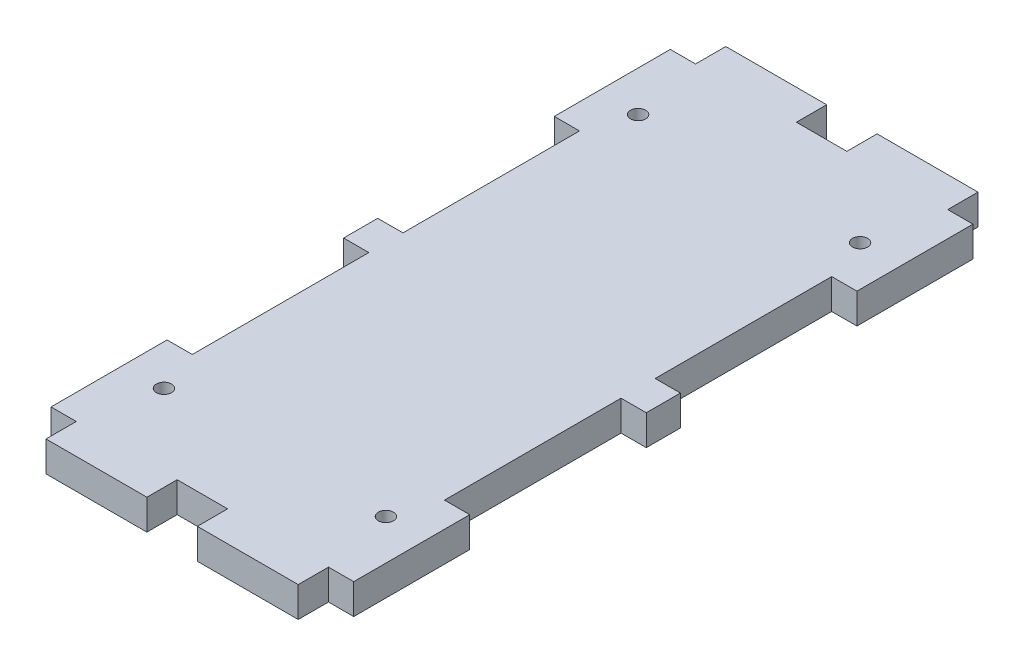
SolidWorks part; units mm, degrees
ref_plane "Plan de face" through (0, 0, 0) normal (0, 0, 1) x (1, 0, 0)
ref_plane "Plan de dessus" through (0, 0, 0) normal (0, 1, 0) x (1, 0, 0)
ref_plane "Plan de droite" through (0, 0, 0) normal (1, 0, 0) x (0, 0, -1)
sketch "Esquisse1" plane through (0, 0, 0) normal (0, 1, 0) x (1, 0, 0)
  line L0 (0, 89.2093) -> (0, -94.1785) construction
  line L1 (-30, 61.38) -> (30, 61.38)
  line L2 (-30, 61.38) -> (-30, -61.38)
  line L3 (-30, -61.38) -> (30, -61.38)
  line L4 (30, 61.38) -> (30, -61.38)
  dimension "D1" = 60
  dimension "D2" = 122.76
  dimension "D3" = 61.38
  dimension "D4" = 30
extrude "Boss.-Extru.1" add sketch "Esquisse1" along normal blind 6
sketch "Esquisse2" plane through (0, 6, 0) normal (0, 1, 0) x (1, 0, 0)
  line L0 (30, 61.38) -> (-30, 61.38) construction
  line L1 (-25, 61.38) -> (-5, 61.38)
  line L2 (-25, 61.38) -> (-25, 67.38)
  line L3 (-25, 67.38) -> (-5, 67.38)
  line L4 (-5, 61.38) -> (-5, 67.38)
  line L6 (5, 61.38) -> (25, 61.38)
  line L7 (5, 61.38) -> (5, 67.38)
  line L8 (5, 67.38) -> (25, 67.38)
  line L9 (25, 61.38) -> (25, 67.38)
  line L10 (-30, 61.38) -> (-30, -61.38) construction
  line L11 (30, -61.38) -> (30, 61.38) construction
  line L12 (-114.0924, 0) -> (165.6917, 0) construction
  line L13 (25, -61.38) -> (25, -67.38)
  line L14 (5, -67.38) -> (25, -67.38)
  line L15 (5, -61.38) -> (5, -67.38)
  line L16 (5, -61.38) -> (25, -61.38)
  line L17 (-5, -61.38) -> (-5, -67.38)
  line L18 (-25, -67.38) -> (-5, -67.38)
  line L19 (-25, -61.38) -> (-25, -67.38)
  line L20 (-25, -61.38) -> (-5, -61.38)
  dimension "D1" = 6
  dimension "D2" = 20
  dimension "D3" = 6
  dimension "D4" = 20
  dimension "D5" = 5
  dimension "D6" = 5
extrude "Boss.-Extru.2" add sketch "Esquisse2" against normal blind 6
sketch "Esquisse3" plane through (0, 6, 0) normal (0, 1, 0) x (1, 0, 0)
  line L0 (73.2715, 0) -> (-73.7315, 0) construction
  line L1 (-60.2107, 47) -> (82.7649, 47) construction
  line L2 (-25, 61.38) -> (-30, 61.38) construction
  line L3 (30, -61.38) -> (30, 61.38) construction
  line L4 (-30, 61.38) -> (-30, -61.38) construction
  circle A0 centre (22, 47) radius 1.5
  circle A1 centre (-22, 47) radius 1.5
  circle A2 centre (-22, -47) radius 1.5
  circle A3 centre (22, -47) radius 1.5
  point P5 (-27.5, 61.38)
  dimension "D3" = 3
  dimension "D4" = 3
  dimension "D5" = 44
  dimension "D6" = 94
  dimension "D1" = 14.38
  dimension "D2" = 8
  dimension "D7" = 8
extrude "Enlèv. mat.-Extru.1" cut sketch "Esquisse3" against normal blind 6
sketch "Esquisse4" plane through (0, 6, 0) normal (0, 1, 0) x (1, 0, 0)
  line L0 (-30, 61.38) -> (-30, -61.38) construction
  line L1 (-30, -3.38) -> (-25, -3.38)
  line L2 (-30, -3.38) -> (-30, -38.38)
  line L3 (-30, -38.38) -> (-25, -38.38)
  line L4 (-25, -3.38) -> (-25, -38.38)
  line L5 (0, 78.1772) -> (0, -74.3107) construction
  line L6 (-30, -61.38) -> (-25, -61.38) construction
  line L7 (25, -3.38) -> (25, -38.38)
  line L8 (30, -38.38) -> (25, -38.38)
  line L9 (30, -3.38) -> (30, -38.38)
  line L10 (30, -3.38) -> (25, -3.38)
  line L11 (-25, 61.38) -> (-30, 61.38) construction
  line L12 (-30, 3.38) -> (-25, 3.38)
  line L13 (-30, 3.38) -> (-30, 38.38)
  line L14 (-30, 38.38) -> (-25, 38.38)
  line L15 (-25, 3.38) -> (-25, 38.38)
  line L16 (25, 3.38) -> (25, 38.38)
  line L17 (30, 38.38) -> (25, 38.38)
  line L18 (30, 3.38) -> (30, 38.38)
  line L19 (30, 3.38) -> (25, 3.38)
  point P9 (-27.5, -61.38)
  dimension "D1" = 5
  dimension "D2" = 35
  dimension "D3" = 23
  dimension "D4" = 35
  dimension "D5" = 23
  dimension "D6" = 5
extrude "Enlèv. mat.-Extru.2" cut sketch "Esquisse4" against normal blind 6
equation "\"D3@Esquisse1\"=\"D2@Esquisse1\"/2"
equation "\"D4@Esquisse1\"=\"D1@Esquisse1\"/2"
